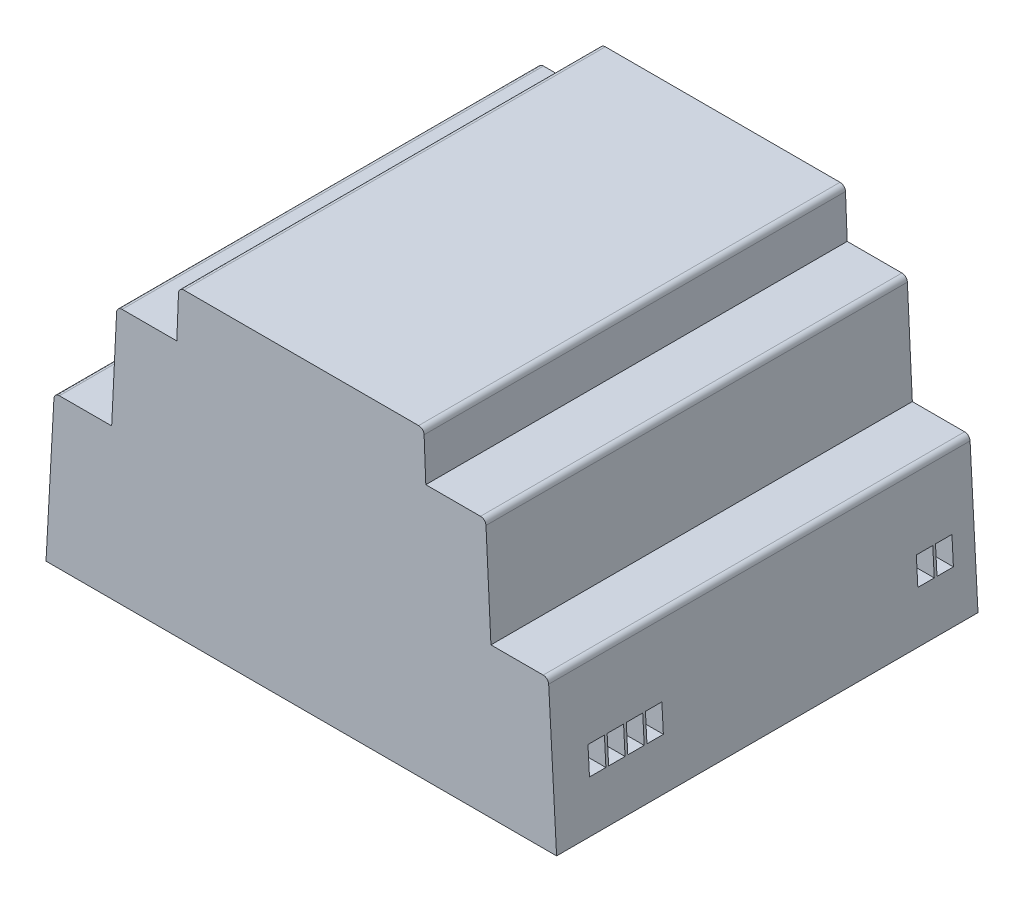
SolidWorks part; units mm, degrees
ref_plane "Front Plane" through (0, 0, 0) normal (0, 0, 1) x (1, 0, 0)
ref_plane "Top Plane" through (0, 0, 0) normal (0, 1, 0) x (1, 0, 0)
ref_plane "Right Plane" through (0, 0, 0) normal (1, 0, 0) x (0, 0, -1)
sketch "Sketch1" plane through (0, 0, 0) normal (0, 0, 1) x (1, 0, 0)
  line L0 (-46.65, 0) -> (46.65, 0)
  line L1 (45.15, 27.4) -> (34.65, 27.4)
  line L2 (45.15, 27.4) -> (46.65, 0)
  line L3 (0, 0) -> (0, 81.2407) construction
  line L4 (34.65, 27.4) -> (33.7, 46.8)
  line L5 (33.7, 46.8) -> (22.75, 46.8)
  line L6 (22.75, 46.8) -> (22.4, 55.5)
  line L7 (22.4, 55.5) -> (-22.4, 55.5)
  line L8 (-22.75, 46.8) -> (-22.4, 55.5)
  line L9 (-33.7, 46.8) -> (-22.75, 46.8)
  line L10 (-34.65, 27.4) -> (-33.7, 46.8)
  line L11 (-45.15, 27.4) -> (-46.65, 0)
  line L12 (-45.15, 27.4) -> (-34.65, 27.4)
  point P12 (0, 55.5)
  dimension "D1" = 93.3
  dimension "D2" = 45.15
  dimension "D3" = 27.4
  dimension "D4" = 34.65
  dimension "D5" = 33.7
  dimension "D6" = 19.4
  dimension "D7" = 22.75
  dimension "D8" = 8.7
  dimension "D9" = 22.4
extrude "Boss-Extrude1" add sketch "Sketch1" along normal blind 77
fillet "Fillet1" radius 1 6 edges at (-45.15, 27.4, 38.5) (-33.7, 46.8, 38.5) (-22.4, 55.5, 38.5) (22.4, 55.5, 38.5) (33.7, 46.8, 38.5) (45.15, 27.4, 38.5)
ref_plane "Plane1" through (46.65, 0, 0) normal (1, 0, 0) x (0, 0, -1)
sketch "Sketch2" plane through (46.65, 0, 0) normal (1, 0, 0) x (0, 0, -1)
  line L0 (-77, 0) -> (0, 0) construction
  line L1 (0, 0) -> (0, 26.4547) construction
  line L5 (-7, 14) -> (-4, 14)
  line L6 (-7, 14) -> (-7, 9)
  line L7 (-7, 9) -> (-4, 9)
  line L8 (-4, 14) -> (-4, 9)
  dimension "D1" = 3
  dimension "D2" = 5
  dimension "D3" = 9
  dimension "D4" = 4
extrude "Cut-Extrude1" cut sketch "Sketch2" against normal blind 10
pattern_linear "LPattern1" count 2 spacing 3.5 along (0, 0, 1) of "Cut-Extrude1"
pattern_linear "LPattern2" count 2 spacing 60 along (0, 0, 1) of "Cut-Extrude1", "LPattern1"
pattern_linear "LPattern4" count 2 spacing 53 along (0, 0, 1) of "LPattern1", "Cut-Extrude1"
